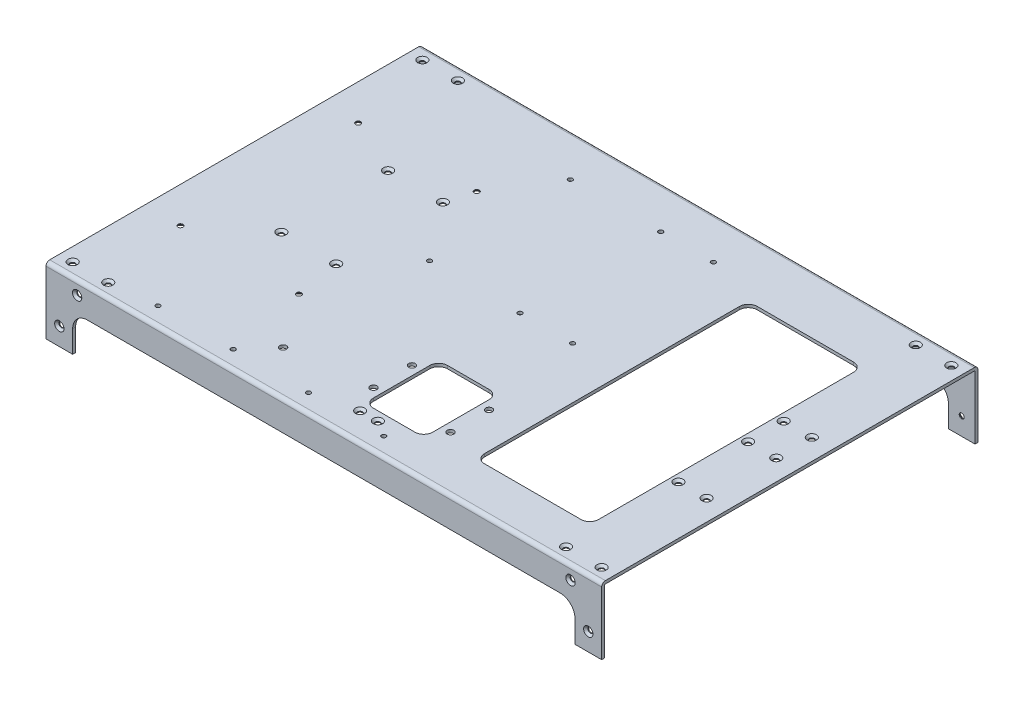
SolidWorks part; units mm, degrees
material "6061-T6 (SS)"
ref_plane "Front Plane" through (0, 0, 0) normal (0, 0, 1) x (1, 0, 0)
ref_plane "Top Plane" through (0, 0, 0) normal (0, 1, 0) x (1, 0, 0)
ref_plane "Right Plane" through (0, 0, 0) normal (1, 0, 0) x (0, 0, -1)
sketch "Sketch1" plane through (0, 0, 0) normal (1, 0, 0) x (0, 0, -1)
  line L0 (125, -100.5) -> (127, -100.5)
  line L1 (-124.5, 0) -> (124.5, 0)
  line L2 (-127, -2.5) -> (-127, -100.5)
  line L3 (-127, -100.5) -> (-125, -100.5)
  line L4 (127, -2.5) -> (127, -100.5)
  line L6 (-125, -100.5) -> (-125, -2.5)
  line L7 (-124.5, -2) -> (124.5, -2)
  line L8 (125, -100.5) -> (125, -2.5)
  arc A0 (-124.5, 0) -> (-127, -2.5) centre (-124.5, -2.5) ccw
  arc A1 (124.5, 0) -> (127, -2.5) centre (124.5, -2.5) cw
  arc A2 (124.5, -2) -> (125, -2.5) centre (124.5, -2.5) cw
  arc A3 (-125, -2.5) -> (-124.5, -2) centre (-124.5, -2.5) cw
  dimension "D1" = 2.5
  dimension "D2" = 250
  dimension "D3" = 2
  dimension "D4" = 100.5
extrude "Boss-Extrude1" add sketch "Sketch1" along normal mid plane 375
sketch "Sketch2" plane through (0, 0, 127) normal (0, 0, 1) x (1, 0, 0)
  line L1 (187.5, -45) -> (187.5, -100.5)
  line L2 (-169.5, -45) -> (-169.5, -30)
  line L3 (-159.5, -20) -> (159.5, -20)
  line L4 (169.5, -45) -> (169.5, -30)
  line L5 (187.5, -2.5) -> (187.5, -100.5) construction
  line L6 (187.5, 0) -> (-187.5, 0) construction
  line L7 (-187.5, -2.5) -> (-187.5, -100.5) construction
  line L8 (169.5, -45) -> (187.5, -45)
  line L9 (187.5, -100.5) -> (-187.5, -100.5)
  line L10 (-187.5, -100.5) -> (-187.5, -45)
  line L11 (-187.5, -45) -> (-169.5, -45)
  arc A0 (159.5, -20) -> (169.5, -30) centre (159.5, -30) cw
  arc A1 (-169.5, -30) -> (-159.5, -20) centre (-159.5, -30) cw
  dimension "D5" = 10
  dimension "D1" = 18
  dimension "D2" = 20
  dimension "D3" = 18
  dimension "D4" = 45
  dimension "D6" = 45
extrude "Cut-Extrude1" cut sketch "Sketch2" against normal through all
sketch "Sketch5" plane through (0, -2, 0) normal (0, -1, 0) x (1, 0, 0)
  line L1 (78.5, 97) -> (143.5, 97)
  line L2 (72.5, 91) -> (72.5, -81)
  line L3 (78.5, -87) -> (143.5, -87)
  line L4 (149.5, 91) -> (149.5, -81)
  line L7 (159.5, -127) -> (-159.5, -127) construction
  line L8 (187.5, 124.5) -> (187.5, -124.5) construction
  line L17 (-187.5, -124.5) -> (-187.5, 124.5) construction
  line L18 (159.5, 127) -> (-159.5, 127) construction
  arc A8 (72.5, -81) -> (78.5, -87) centre (78.5, -81) ccw
  arc A9 (143.5, -87) -> (149.5, -81) centre (143.5, -81) ccw
  arc A10 (149.5, 91) -> (143.5, 97) centre (143.5, 91) ccw
  arc A11 (78.5, 97) -> (72.5, 91) centre (78.5, 91) ccw
  dimension "D5" = 6
  dimension "D1" = 30
  dimension "D2" = 40
  dimension "D3" = 38
  dimension "D4" = 260
extrude "Cut-Extrude4" cut sketch "Sketch5" against normal blind 10
sketch "Sketch6" plane through (0, 0, -127) normal (0, 0, -1) x (-1, 0, 0)
  line L0 (-187.5, 0) -> (187.5, 0) construction
  line L1 (-187.5, -45) -> (-187.5, -2.5) construction
  line L2 (187.5, -45) -> (187.5, -2.5) construction
  circle A0 centre (-178.5, -33) radius 1.5
  circle A1 centre (-178.5, -9) radius 1.5 construction
  circle A2 centre (-166.5, -9) radius 1.5
  circle A3 centre (166.5, -9) radius 1.5
  circle A4 centre (178.5, -9) radius 1.5 construction
  circle A5 centre (178.5, -33) radius 1.5
  dimension "D1" = 3
  dimension "D6" = 9
  dimension "D2" = 9
  dimension "D3" = 9
  dimension "D4" = 33
  dimension "D7" = 21
  dimension "D8" = 21
extrude "Cut-Extrude5" cut sketch "Sketch6" against normal through all
sketch "Sketch9" plane through (0, 0, 0) normal (0, 1, 0) x (1, 0, 0)
  line L0 (-187.5, 124.5) -> (-187.5, -124.5) construction
  line L1 (187.5, 124.5) -> (187.5, -124.5) construction
  line L2 (187.5, 127) -> (-187.5, 127) construction
  line L3 (187.5, -127) -> (-187.5, -127) construction
  circle A0 centre (-178.5, 118) radius 1.5
  circle A1 centre (-154.5, 118) radius 1.5
  circle A2 centre (154.5, 118) radius 1.5
  circle A3 centre (178.5, 118) radius 1.5
  circle A4 centre (178.5, -118) radius 1.5
  circle A5 centre (154.5, -118) radius 1.5
  circle A6 centre (-154.5, -118) radius 1.5
  circle A7 centre (-178.5, -118) radius 1.5
  circle A8 centre (-125.5, 41.85) radius 1.5
  circle A9 centre (-88.5, 41.85) radius 1.5
  circle A10 centre (-125.5, -30.15) radius 1.5
  circle A11 centre (-88.5, -30.15) radius 1.5
  circle A12 centre (154.5, 28.85) radius 1.5
  circle A13 centre (173.5, 4.85) radius 1.5
  circle A14 centre (154.5, 4.85) radius 1.5
  circle A15 centre (173.5, 28.85) radius 1.5
  circle A16 centre (154.5, -42.15) radius 1.5
  circle A17 centre (173.5, -42.15) radius 1.5
  dimension "D1" = 3
  dimension "D2" = 9
  dimension "D3" = 33
  dimension "D4" = 9
  dimension "D5" = 33
  dimension "D6" = 9
  dimension "D7" = 9
extrude "Cut-Extrude8" cut sketch "Sketch9" against normal blind 10
sketch "Sketch19" plane through (0, 0, 0) normal (0, 1, 0) x (1, 0, 0)
  circle A0 centre (2.31, 98.065) radius 1.5
  circle A1 centre (-58.69, 98.065) radius 1.5
  circle A2 centre (37.83, 98.065) radius 1.5
  circle A3 centre (-58.69, 3.065) radius 1.5
  circle A4 centre (37.83, 3.065) radius 1.5
  circle A9 centre (2.31, 3.065) radius 1.5
  circle A10 centre (-163.3, 59.5) radius 1.5
  circle A11 centre (-163.3, -60.5) radius 1.5
  circle A12 centre (-83.3, -60.5) radius 1.5
  circle A13 centre (-83.3, 59.5) radius 1.5
  circle A14 centre (-124.1, -114.8527) radius 1.5
  circle A15 centre (-73.3, -114.8527) radius 1.5
  circle A16 centre (-22.5, -114.8527) radius 1.5
  circle A17 centre (28.3, -114.8527) radius 1.5
  dimension "D1" = 3
  dimension "D2" = 61
extrude "Cut-Extrude9" cut sketch "Sketch19" against normal blind 10
sketch "Sketch20" plane through (0, 0, -127) normal (0, 0, -1) x (-1, 0, 0)
  circle A0 centre (-39.5, -8) radius 1.75
  circle A1 centre (47.5, -8) radius 1.75
  circle A2 centre (134.5, -8) radius 1.75
  dimension "D1" = 3.5
extrude "Cut-Extrude10" cut sketch "Sketch20" against normal blind 10
hole_wizard "CSK for M3 Flat Head Machine Screw1" positions "Sketch22" profile "Sketch21" countersink size "M3" standard "Ansi Metric"
sketch "Sketch22" plane through (0, 0, 127) normal (0, 0, 1) x (1, 0, 0)
  point P0 (-166.5, -9)
  point P1 (166.5, -9)
  point P4 (178.5, -33)
  point P7 (-178.5, -33)
sketch "Sketch21" plane through (-166.5, -9, 127) normal (1, 0, 0) x (0, -1, 0)
  line L0 (0, 0) -> (0, 11.0215)
  line L1 (0, 11.0215) -> (1.7, 10)
  line L2 (1.7, 10) -> (1.7, 1.45)
  line L3 (1.7, 1.45) -> (3.15, 0)
  line L5 (3.15, 0) -> (0, 0)
  line L6 (-1.7, 1.45) -> (-3.15, 0) construction
  line L10 (0, 11.0215) -> (-1.7, 10) construction
  line L11 (0, -6.35) -> (0, 107.95) construction
  dimension "Hole Dia." = 3.4
  dimension "Hole Depth" = 10
  dimension "Near C'Sink Dia." = 6.3
  dimension "Near C'Sink Angle" = 90
  dimension "Drill Angle" = 118
hole_wizard "CSK for M3 Flat Head Machine Screw2" positions "Sketch24" profile "Sketch25" countersink size "M3" standard "Ansi Metric"
sketch "Sketch24" plane through (0, 0, -127) normal (0, 0, -1) x (-1, 0, 0)
  point P0 (-166.5, -9)
  point P1 (178.5, -33)
  point P5 (166.5, -9)
  point P8 (-178.5, -33)
sketch "Sketch25" plane through (166.5, -9, -127) normal (1, 0, 0) x (0, 1, 0)
  line L0 (0, 0) -> (0, 11.0215)
  line L1 (0, 11.0215) -> (1.7, 10)
  line L2 (1.7, 10) -> (1.7, 1.45)
  line L3 (1.7, 1.45) -> (3.15, 0)
  line L5 (3.15, 0) -> (0, 0)
  line L6 (-1.7, 1.45) -> (-3.15, 0) construction
  line L10 (0, 11.0215) -> (-1.7, 10) construction
  line L11 (0, -6.35) -> (0, 107.95) construction
  dimension "Hole Dia." = 3.4
  dimension "Hole Depth" = 10
  dimension "Near C'Sink Dia." = 6.3
  dimension "Near C'Sink Angle" = 90
  dimension "Drill Angle" = 118
hole_wizard "CSK for M3 Flat Head Machine Screw3" positions "Sketch27" profile "Sketch26" countersink size "M3" standard "Ansi Metric"
sketch "Sketch27" plane through (0, 0, 0) normal (0, 1, 0) x (-1, 0, 0)
  point P0 (88.5, -41.85)
  point P1 (178.5, -118)
  point P4 (154.5, -118)
  point P7 (125.5, -41.85)
  point P10 (125.5, 30.15)
  point P13 (88.5, 30.15)
  point P16 (178.5, 118)
  point P19 (154.5, 118)
  point P22 (-154.5, 118)
  point P25 (-178.5, 118)
  point P28 (-154.5, 42.15)
  point P31 (-173.5, 42.15)
  point P34 (-173.5, -4.85)
  point P37 (-154.5, -4.85)
  point P40 (-173.5, -28.85)
  point P43 (-154.5, -28.85)
  point P46 (-178.5, -118)
  point P49 (-154.5, -118)
sketch "Sketch26" plane through (-88.5, 0, -41.85) normal (1, 0, 0) x (0, 0, 1)
  line L0 (0, 0) -> (0, 11.0215)
  line L1 (0, 11.0215) -> (1.7, 10)
  line L2 (1.7, 10) -> (1.7, 1.45)
  line L3 (1.7, 1.45) -> (3.15, 0)
  line L5 (3.15, 0) -> (0, 0)
  line L6 (-1.7, 1.45) -> (-3.15, 0) construction
  line L10 (0, 11.0215) -> (-1.7, 10) construction
  line L11 (0, -6.35) -> (0, 107.95) construction
  dimension "Hole Dia." = 3.4
  dimension "Hole Depth" = 10
  dimension "Near C'Sink Dia." = 6.3
  dimension "Near C'Sink Angle" = 90
  dimension "Drill Angle" = 118
sketch "Sketch28" plane through (0, 0, 0) normal (0, 1, 0) x (-1, 0, 0)
  line L0 (-187.5, 127) -> (187.5, 127) construction
  line L1 (-8.5, 52) -> (-36.5, 52)
  line L2 (-2.5, 58) -> (-2.5, 96)
  line L3 (-8.5, 102) -> (-36.5, 102)
  line L4 (-42.5, 58) -> (-42.5, 96)
  line L5 (187.5, -124.5) -> (187.5, 124.5) construction
  arc A0 (-36.5, 102) -> (-42.5, 96) centre (-36.5, 96) ccw
  arc A1 (-36.5, 52) -> (-42.5, 58) centre (-36.5, 58) cw
  arc A2 (-8.5, 52) -> (-2.5, 58) centre (-8.5, 58) ccw
  arc A3 (-2.5, 96) -> (-8.5, 102) centre (-8.5, 96) ccw
  circle A4 centre (57.5, 97) radius 2.25
  dimension "D5" = 6
  dimension "D6" = 60
  dimension "D8" = 4.5
  dimension "D1" = 25
  dimension "D2" = 50
  dimension "D3" = 190
  dimension "D4" = 230
  dimension "D7" = 30
extrude "Cut-Extrude11" cut sketch "Sketch28" against normal blind 10
hole_wizard "CSK for M3 Flat Head Machine Screw4" positions "Sketch30" profile "Sketch29" countersink size "M3" standard "Ansi Metric"
sketch "Sketch30" plane through (0, -2, 0) normal (0, -1, 0) x (1, 0, 0)
  point P0 (-163.3, -59.5)
  point P1 (-163.3, 60.5)
  point P4 (-83.3, 60.5)
  point P7 (-83.3, -59.5)
sketch "Sketch29" plane through (-163.3, -2, -59.5) normal (1, 0, 0) x (0, 0, -1)
  line L0 (0, 0) -> (0, 11.0215)
  line L1 (0, 11.0215) -> (1.7, 10)
  line L2 (1.7, 10) -> (1.7, 1.45)
  line L3 (1.7, 1.45) -> (3.15, 0)
  line L5 (3.15, 0) -> (0, 0)
  line L6 (-1.7, 1.45) -> (-3.15, 0) construction
  line L10 (0, 11.0215) -> (-1.7, 10) construction
  line L11 (0, -6.35) -> (0, 107.95) construction
  dimension "Hole Dia." = 3.4
  dimension "Hole Depth" = 10
  dimension "Near C'Sink Dia." = 6.3
  dimension "Near C'Sink Angle" = 90
  dimension "Drill Angle" = 118
sketch "Sketch31" plane through (0, 0, 0) normal (0, 1, 0) x (1, 0, 0)
  line L0 (42.5, -96) -> (42.5, -58) construction
  line L1 (2.5, -58) -> (2.5, -96) construction
  line L2 (-3.5, -64) -> (-3.5, -90) construction
  line L3 (-3.5, -77) -> (2.5, -77) construction
  circle A0 centre (-3.5, -64) radius 2.25
  circle A1 centre (-3.5, -90) radius 2.25
  circle A2 centre (48.5, -64) radius 2.25
  circle A3 centre (48.5, -90) radius 2.25
  circle A4 centre (17.5, -108) radius 1.5
  circle A5 centre (5.5, -108) radius 1.5
  dimension "D1" = 3
  dimension "D2" = 4.5
  dimension "D3" = 6
  dimension "D4" = 6
  dimension "D5" = 26
extrude "Cut-Extrude12" cut sketch "Sketch31" against normal blind 10
hole_wizard "CSK for M3 Flat Head Machine Screw5" positions "Sketch34" profile "Sketch33" countersink size "M3" standard "Ansi Metric"
sketch "Sketch34" plane through (0, 0, 0) normal (0, 1, 0) x (-1, 0, 0)
  point P0 (-5.5, 108)
  point P1 (-17.5, 108)
sketch "Sketch33" plane through (5.5, 0, 108) normal (1, 0, 0) x (0, 0, 1)
  line L0 (0, 0) -> (0, 11.0215)
  line L1 (0, 11.0215) -> (1.7, 10)
  line L2 (1.7, 10) -> (1.7, 1.45)
  line L3 (1.7, 1.45) -> (3.15, 0)
  line L5 (3.15, 0) -> (0, 0)
  line L6 (-1.7, 1.45) -> (-3.15, 0) construction
  line L10 (0, 11.0215) -> (-1.7, 10) construction
  line L11 (0, -6.35) -> (0, 107.95) construction
  dimension "Hole Dia." = 3.4
  dimension "Hole Depth" = 10
  dimension "Near C'Sink Dia." = 6.3
  dimension "Near C'Sink Angle" = 90
  dimension "Drill Angle" = 118
